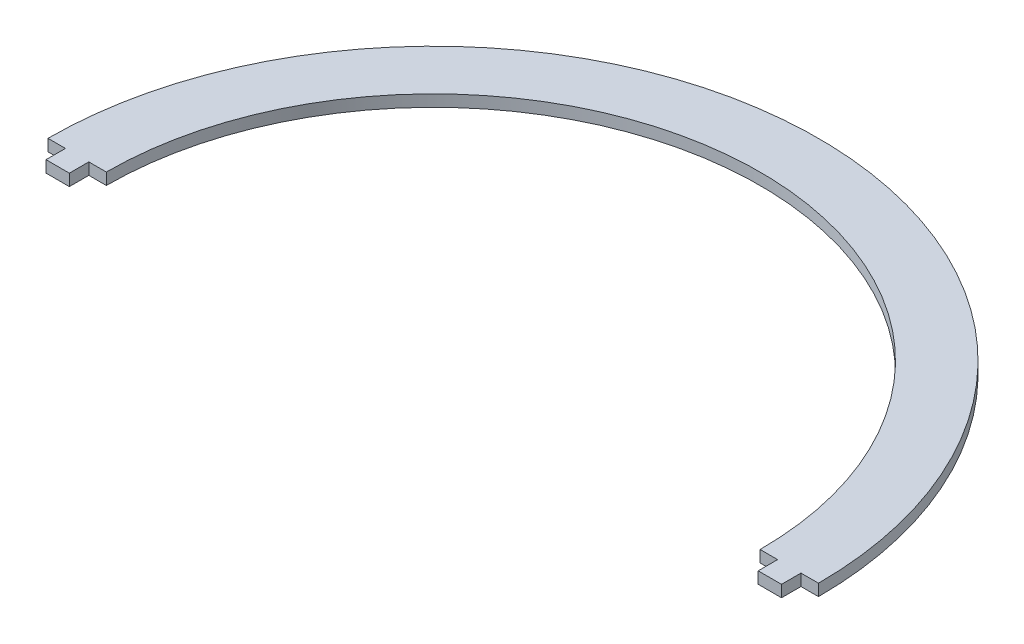
SolidWorks part; units mm, degrees
ref_plane "Front Plane" through (0, 0, 0) normal (0, 0, 1) x (1, 0, 0)
ref_plane "Top Plane" through (0, 0, 0) normal (0, 1, 0) x (1, 0, 0)
ref_plane "Right Plane" through (0, 0, 0) normal (1, 0, 0) x (0, 0, -1)
sketch "Sketch1" plane through (0, 0, 0) normal (0, 1, 0) x (1, 0, 0)
  line L0 (-94.5, 0) -> (-88.5, 0)
  line L1 (-88.5, 0) -> (-88.5, 5)
  line L2 (-88.5, 5) -> (-84, 5)
  line L3 (84, 5) -> (88.5, 5)
  line L4 (88.5, 5) -> (88.5, 0)
  line L5 (88.5, 0) -> (94.5, 0)
  line L6 (94.5, 0) -> (94.5, 5)
  line L7 (94.5, 5) -> (99, 5)
  line L8 (-99, 5) -> (-94.5, 5)
  line L9 (-94.5, 5) -> (-94.5, 0)
  arc A0 (-84, 5) -> (84, 5) centre (0, 5) cw
  arc A1 (99, 5) -> (-99, 5) centre (0, 5) ccw
  dimension "D1" = 6
  dimension "D2" = 15
  dimension "D3" = 5
  dimension "D4" = 177
extrude "Boss-Extrude1" add sketch "Sketch1" along normal mid plane 3
